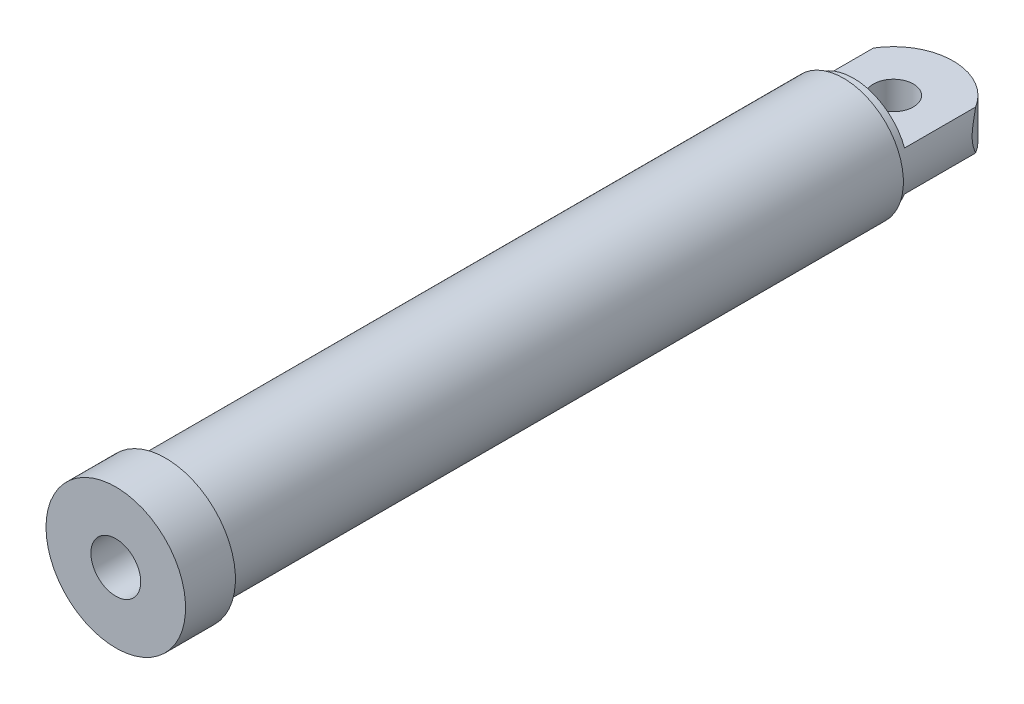
SolidWorks part; units mm, degrees
material "AISI 4340 Steel, normalized"
ref_plane "Front Plane" through (0, 0, 0) normal (0, 0, 1) x (1, 0, 0)
ref_plane "Top Plane" through (0, 0, 0) normal (0, 1, 0) x (1, 0, 0)
ref_plane "Right Plane" through (0, 0, 0) normal (1, 0, 0) x (0, 0, -1)
sketch "Sketch1" plane through (0, 0, 0) normal (0, 1, 0) x (1, 0, 0)
  line L0 (0, 0) -> (0, -780) construction
  line L1 (0, -780) -> (70, -780) construction
  line L2 (70, -780) -> (70, -730)
  line L3 (70, -730) -> (60, -730)
  line L4 (60, -730) -> (60, -40)
  line L5 (60, -40) -> (0, -40)
  line L6 (70, -780) -> (25, -780)
  line L7 (25, -780) -> (25, -700)
  line L8 (25, -700) -> (45, -700)
  line L9 (45, -700) -> (45, -60)
  line L10 (45, -60) -> (0, -60)
  line L11 (0, -60) -> (0, -40)
  circle A0 centre (0, 0) radius 20 construction
  circle A1 centre (0, 0) radius 60 construction
  dimension "D5" = 120
  dimension "D6" = 40
  dimension "D1" = 780
  dimension "D2" = 120
  dimension "D3" = 10
  dimension "D4" = 50
  dimension "D7" = 80
  dimension "D8" = 15
  dimension "D9" = 50
  dimension "D10" = 20
  dimension "D11" = 40
revolve "Revolve1" add sketch "Sketch1" angle 360 about L0
sketch "Sketch2" plane through (0, 0, 0) normal (0, 1, 0) x (1, 0, 0)
  line L0 (60, -40) -> (60, 0)
  line L1 (-60, -40) -> (-60, 0)
  line L2 (60, -40) -> (-60, -40)
  circle A0 centre (0, 0) radius 20
  circle A1 centre (0, 0) radius 20 construction
  arc A2 (60, 0) -> (-60, 0) centre (0, 0) ccw
  circle A3 centre (0, 0) radius 60 construction
extrude "Boss-Extrude1" add sketch "Sketch2" along normal mid plane 40
sketch "Sketch3" plane through (0, 0, 40) normal (0, 0, -1) x (-1, 0, 0)
  circle A0 centre (0, 0) radius 55
  circle A2 centre (0, 0) radius 63.2456
  arc A3 (56.5685, 20) -> (-56.5685, 20) centre (0, 0) ccw construction
  dimension "D1" = 5
extrude "Cut-Extrude1" cut sketch "Sketch3" along normal through all and the other way blind 10
